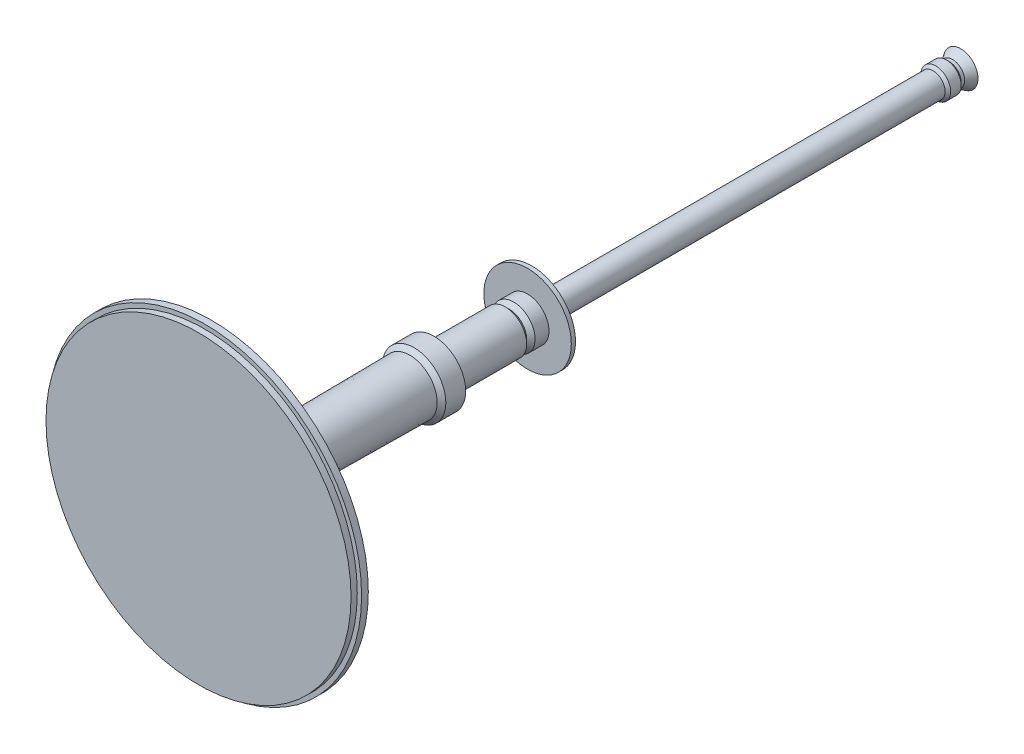
SolidWorks part; units mm, degrees
ref_plane "Front Plane" through (0, 0, 0) normal (0, 0, 1) x (1, 0, 0)
ref_plane "Top Plane" through (0, 0, 0) normal (0, 1, 0) x (1, 0, 0)
ref_plane "Right Plane" through (0, 0, 0) normal (1, 0, 0) x (0, 0, -1)
sketch "Sketch1" plane through (0, 0, 0) normal (1, 0, 0) x (0, 0, -1)
  line L0 (31.8024, 848.4909) -> (1294.8478, 848.4909) construction
sketch "Sketch12" plane through (0, 0, 0) normal (1, 0, 0) x (0, 0, -1)
  line L0 (0, 0) -> (4052.5471, 0) construction
  line L1 (996.9798, 0) -> (996.9798, 448.1544)
  line L2 (996.9798, 448.1544) -> (1015.3095, 448.1544)
  line L3 (1015.3095, 448.1544) -> (1015.3095, 460.8441)
  line L4 (1015.3095, 460.8441) -> (1035.0491, 460.8441)
  line L5 (1035.0491, 460.8441) -> (1035.0491, 448.1544)
  line L6 (1035.0491, 448.1544) -> (1035.0491, 438.419)
  line L7 (1035.0491, 438.419) -> (1049.7394, 438.419)
  line L8 (1049.7394, 438.419) -> (1049.7394, 107.8627)
  line L9 (1049.7394, 107.8627) -> (1082.4718, 107.8627)
  line L10 (1082.4718, 107.8627) -> (1082.4718, 93.3164)
  line L11 (1082.4718, 93.3164) -> (1090.9331, 84.8551)
  line L12 (1090.9331, 84.8551) -> (1156.2801, 84.8551)
  line L13 (1156.2801, 84.8551) -> (1156.2801, 76.4115)
  line L14 (1156.2801, 76.4115) -> (1617.5893, 80.6333)
  line L15 (1617.5893, 80.6333) -> (1630.2724, 93.3164)
  line L16 (1630.2724, 93.3164) -> (1688.6653, 93.3164)
  line L17 (1688.6653, 93.3164) -> (1688.6653, 62.9541)
  line L18 (1688.6653, 62.9541) -> (1898.2163, 62.9541)
  line L19 (1898.2163, 62.9541) -> (1910.5755, 50.595)
  line L20 (1910.5755, 50.595) -> (1922.9346, 62.9541)
  line L21 (1922.9346, 62.9541) -> (1950.9344, 62.9541)
  line L22 (1950.9344, 62.9541) -> (1963.7925, 62.9541)
  line L23 (1963.7925, 62.9541) -> (1963.7925, 116.1711)
  line L24 (1963.7925, 116.1711) -> (1963.7925, 128.5303)
  line L25 (1963.7925, 128.5303) -> (1976.1517, 128.5303)
  line L26 (1976.1517, 128.5303) -> (1976.1517, 93.3164)
  line L27 (1976.1517, 93.3164) -> (1983.4248, 100.5895)
  line L28 (1983.4248, 100.5895) -> (1983.4248, 35.6642)
  line L29 (1983.4248, 35.6642) -> (3155.0972, 35.6642)
  line L30 (3155.0972, 35.6642) -> (3163.146, 43.713)
  line L31 (3163.146, 43.713) -> (3194.167, 43.713)
  line L32 (3194.167, 43.713) -> (3202.2158, 35.6642)
  line L33 (3202.2158, 35.6642) -> (3212.3996, 35.6642)
  line L34 (3212.3996, 35.6642) -> (3236.7097, 50.595)
  line L35 (3236.7097, 50.595) -> (3236.7097, 0)
  line L36 (996.9798, 0) -> (3236.7097, 0)
revolve "Revolve2" add sketch "Sketch12" angle 360 about L0
